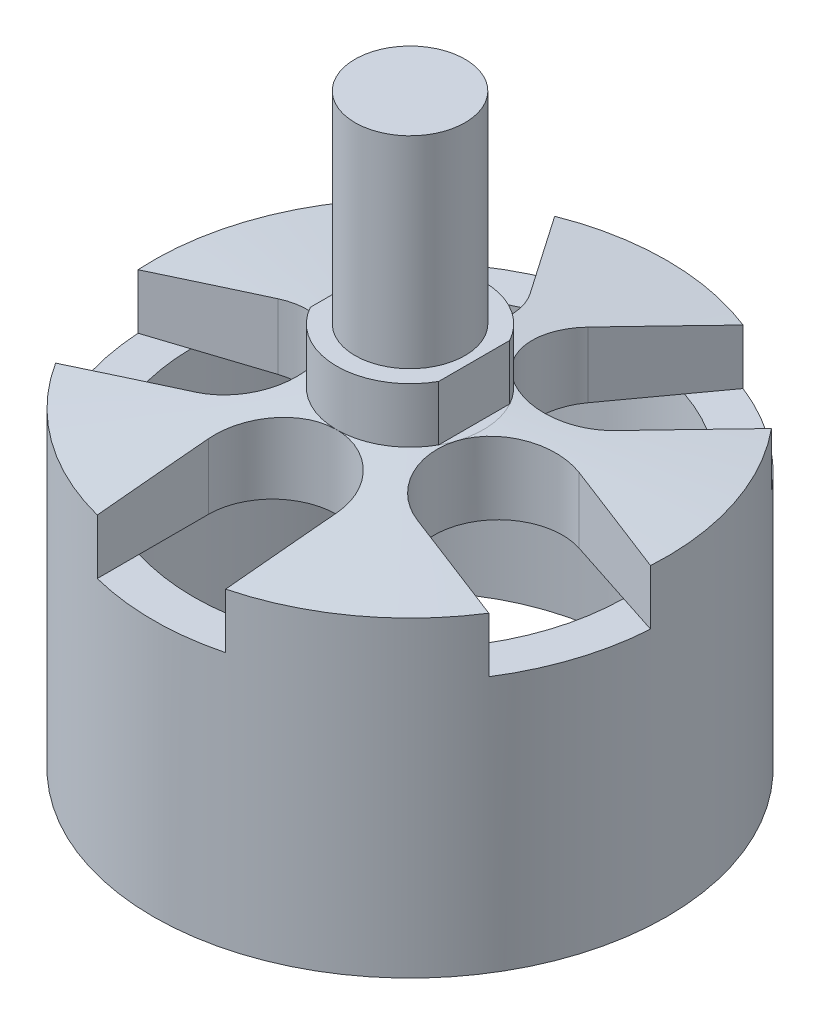
SolidWorks part; units mm, degrees
ref_plane "Спереди" through (0, 0, 0) normal (0, 0, 1) x (1, 0, 0)
ref_plane "Сверху" through (0, 0, 0) normal (0, 1, 0) x (1, 0, 0)
ref_plane "Справа" through (0, 0, 0) normal (1, 0, 0) x (0, 0, -1)
sketch "Эскиз1" plane through (0, 0, 0) normal (0, 1, 0) x (1, 0, 0)
  circle A0 centre (0, 0) radius 14
  circle A1 centre (0, 0) radius 11.8
  dimension "D1" = 28
  dimension "D2" = 2.2
extrude "Бобышка-Вытянуть1" add sketch "Эскиз1" along normal blind 14
sketch "Эскиз2" plane through (0, 14, 0) normal (0, 1, 0) x (1, 0, 0)
  circle A0 centre (0, 0) radius 14
extrude "Бобышка-Вытянуть2" add sketch "Эскиз2" along normal blind 4
chamfer "Фаска1" distance 1 distance2 10 1 edges at (0, 18, 14)
sketch "Эскиз3" plane through (0, 18, 0) normal (0, 1, 0) x (1, 0, 0)
  circle A0 centre (0, 0) radius 4
extrude "Бобышка-Вытянуть3" add sketch "Эскиз3" along normal blind 3
sketch "Эскиз4" plane through (0, 21, 0) normal (0, 1, 0) x (1, 0, 0)
  circle A0 centre (0, 0) radius 3
  dimension "D1" = 6
extrude "Бобышка-Вытянуть4" add sketch "Эскиз4" along normal blind 11
sketch "Эскиз5" plane through (0, 21, 0) normal (0, 1, 0) x (1, 0, 0)
  line L1 (-9.5797, 5.5198) -> (-3.5, 5.5198)
  line L2 (-9.5797, 5.5198) -> (-9.5797, -6.3731)
  line L3 (-9.5797, -6.3731) -> (-3.5, -6.3731)
  line L4 (-3.5, 5.5198) -> (-3.5, -6.3731)
  line L5 (3.5, -6.3731) -> (8.0331, -6.3731)
  line L6 (3.5, -6.3731) -> (3.5, 6.6397)
  line L7 (3.5, 6.6397) -> (8.0331, 6.6397)
  line L8 (8.0331, -6.3731) -> (8.0331, 6.6397)
  dimension "D1" = 3.5
  dimension "D2" = 3.5
extrude "Вырез-Вытянуть1" cut sketch "Эскиз5" against normal blind 3
sketch "Эскиз6" plane through (0, 18, 0) normal (0, 1, 0) x (1, 0, 0)
  line L0 (0, 0) -> (0, -7.5) construction
  line L1 (-3.5, -7.5) -> (-3.5, -15.706)
  line L2 (-3.5, -15.706) -> (3.5, -15.706)
  line L3 (3.5, -15.706) -> (3.5, -7.5)
  circle A0 centre (0, 0) radius 7.5 construction
  arc A1 (3.5, -7.5) -> (-3.5, -7.5) centre (0, -7.5) ccw
  dimension "D1" = 15
  dimension "D2" = 7
extrude "Вырез-Вытянуть2" cut sketch "Эскиз6" against normal blind 4
pattern_circular "Круговой массив1" count 5 over 360 about axis through (0, 0, 0) along (0, 1, 0) of "Вырез-Вытянуть2"
